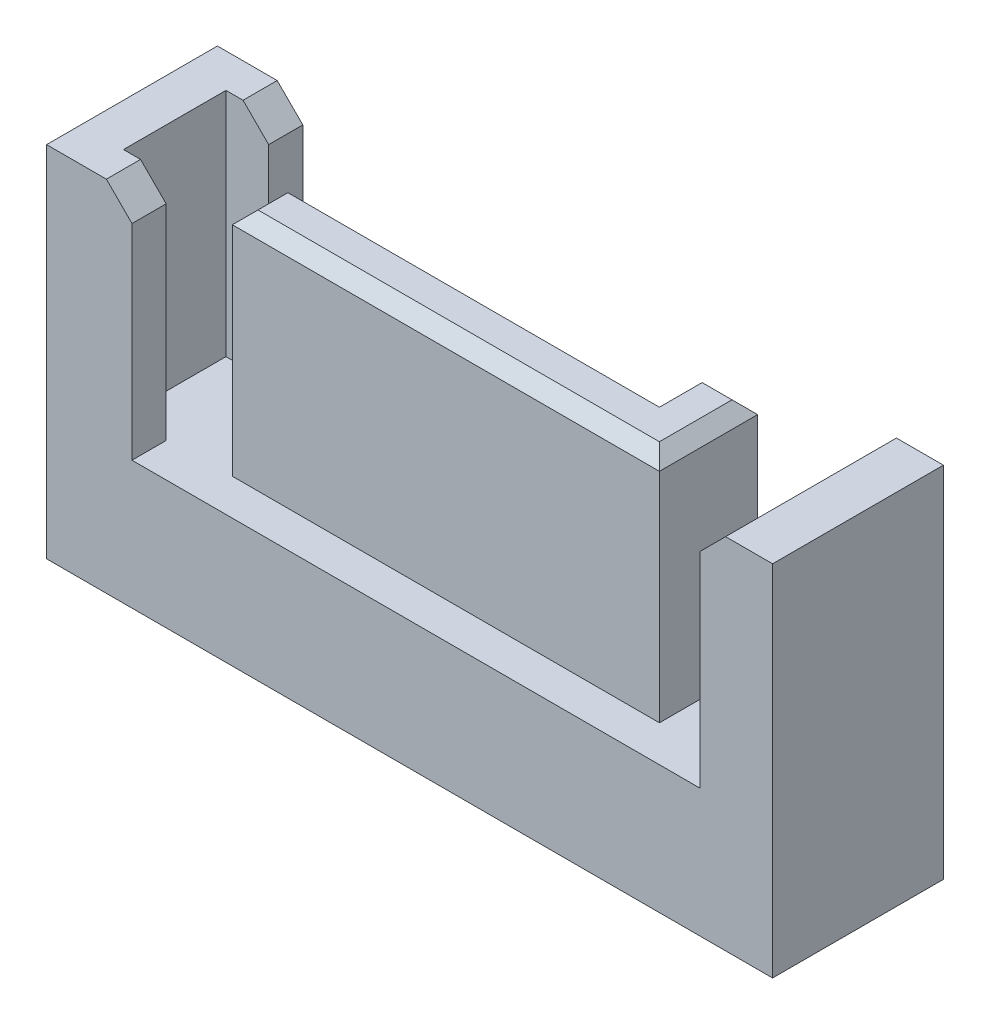
SolidWorks part; units mm, degrees
ref_plane "Alzado" through (0, 0, 0) normal (0, 0, 1) x (1, 0, 0)
ref_plane "Planta" through (0, 0, 0) normal (0, 1, 0) x (1, 0, 0)
ref_plane "Vista lateral" through (0, 0, 0) normal (1, 0, 0) x (0, 0, -1)
sketch "Croquis1" plane through (0, 0, 0) normal (0, 1, 0) x (1, 0, 0)
  line L1 (-8.5, 2) -> (8.5, 2)
  line L2 (-8.5, 2) -> (-8.5, -2)
  line L3 (-8.5, -2) -> (8.5, -2)
  line L4 (8.5, 2) -> (8.5, -2)
  dimension "D1" = 17
  dimension "D2" = 4
  dimension "D3" = 2
  dimension "D4" = 8.5
extrude "Extruir1" add sketch "Croquis1" along normal blind 8.4
sketch "Croquis2" plane through (0, 8.4, 0) normal (0, 1, 0) x (-1, 0, 0)
  line L0 (-8.5, -2) -> (8.5, -2) construction
  line L1 (-6.8, -2) -> (6.5, -2)
  line L2 (-6.8, -2) -> (-6.8, 2)
  line L3 (-6.8, 2) -> (6.5, 2)
  line L4 (6.5, -2) -> (6.5, -1.2)
  line L5 (8.5, 2) -> (-8.5, 2) construction
  line L6 (-8.5, 2) -> (-8.5, -2) construction
  line L7 (6.5, -1.2) -> (7.5, -1.2)
  line L9 (6.5, 1.2) -> (7.5, 1.2)
  line L10 (7.5, -1.2) -> (7.5, 1.2)
  line L11 (8.5, -2) -> (8.5, 2) construction
  line L12 (6.5, 1.2) -> (6.5, 2)
  dimension "D1" = 1.7
  dimension "D2" = 2
  dimension "D3" = 1
  dimension "D4" = 0.8
  dimension "D5" = 0.8
extrude "Cortar-Extruir1" cut sketch "Croquis2" against normal blind 5.4
chamfer "Chaflán1" distance 0.6 angle 45 3 edges at (-6.5, 8.4, 1.6) (-6.5, 8.4, -1.6) (6.8, 8.4, 0)
sketch "Croquis3" plane through (0, 3, 0) normal (0, 1, 0) x (-1, 0, 0)
  line L0 (-5, -1.15) -> (-5, 1.15)
  line L1 (-5, 1.15) -> (5, 1.15)
  line L2 (5, 1.15) -> (5, -0.15)
  line L3 (5, -0.15) -> (-3.7, -0.15)
  line L4 (-3.7, -0.15) -> (-3.7, -1.15)
  line L5 (-3.7, -1.15) -> (-5, -1.15)
  line L6 (8.5, -2) -> (8.5, 2) construction
  line L8 (6.5, 2) -> (-6.8, 2) construction
  dimension "D1" = 10
  dimension "D2" = 2.3
  dimension "D3" = 1.3
  dimension "D4" = 1.3
  dimension "D5" = 3.5
  dimension "D6" = 0.85
extrude "Extruir2" add sketch "Croquis3" along normal blind 5.4
chamfer "Chaflán2" distance 0.3 angle 45 6 edges at (5, 8.4, 0) (4.35, 8.4, -1.15) (3.7, 8.4, -0.65) (-0.65, 8.4, -0.15) (-5, 8.4, 0.5) (0, 8.4, 1.15)
